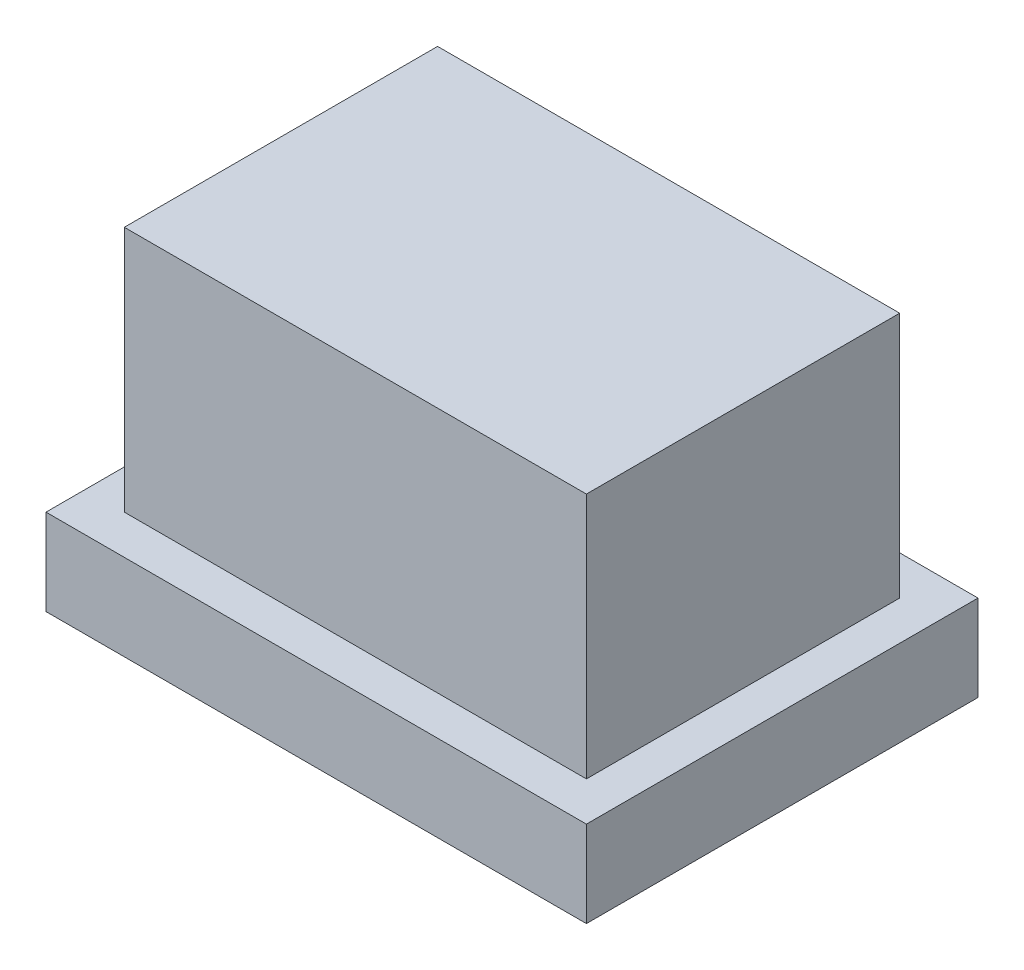
SolidWorks part; units mm, degrees
ref_plane "Alzado" through (0, 0, 0) normal (0, 0, 1) x (1, 0, 0)
ref_plane "Planta" through (0, 0, 0) normal (0, 1, 0) x (1, 0, 0)
ref_plane "Vista lateral" through (0, 0, 0) normal (1, 0, 0) x (0, 0, -1)
sketch "Croquis2" plane through (0, 0, 0) normal (0, 1, 0) x (1, 0, 0)
  line L1 (6.2447, -4.2179) -> (-7.5553, -4.2179)
  line L2 (6.2447, -4.2179) -> (6.2447, 5.7821)
  line L3 (6.2447, 5.7821) -> (-7.5553, 5.7821)
  line L4 (-7.5553, -4.2179) -> (-7.5553, 5.7821)
  dimension "D1" = 13.8
  dimension "D2" = 10
extrude "Saliente-Extruir1" add sketch "Croquis2" along normal blind 2.2
sketch "Croquis3" plane through (0, 2.2, 0) normal (0, 1, 0) x (1, 0, 0)
  line L8 (5.2447, -3.2179) -> (5.2447, 4.7821)
  line L9 (5.2447, 4.7821) -> (-6.5553, 4.7821)
  line L10 (-6.5553, 4.7821) -> (-6.5553, -3.2179)
  line L11 (-6.5553, -3.2179) -> (5.2447, -3.2179)
  line L12 (5.2447, -3.2179) -> (5.2447, 4.7821)
  line L13 (5.2447, 4.7821) -> (-6.5553, 4.7821)
  line L14 (-6.5553, 4.7821) -> (-6.5553, -3.2179)
  line L15 (-6.5553, -3.2179) -> (5.2447, -3.2179)
  dimension "D1" = 1
extrude "Saliente-Extruir2" add sketch "Croquis3" along normal blind 6.3
sketch "Croquis4" plane through (0, 0, 0) normal (0, -1, 0) x (1, 0, 0)
  line L0 (-7.5553, -0.7821) -> (6.2447, -0.7821) construction
  line L1 (-7.5553, -5.7821) -> (-7.5553, 4.2179) construction
  line L2 (6.2447, 4.2179) -> (6.2447, -5.7821) construction
  circle A0 centre (-0.6553, -0.7821) radius 3.5
  dimension "D1" = 7
extrude "Cortar-Extruir1" cut sketch "Croquis4" against normal blind 8
